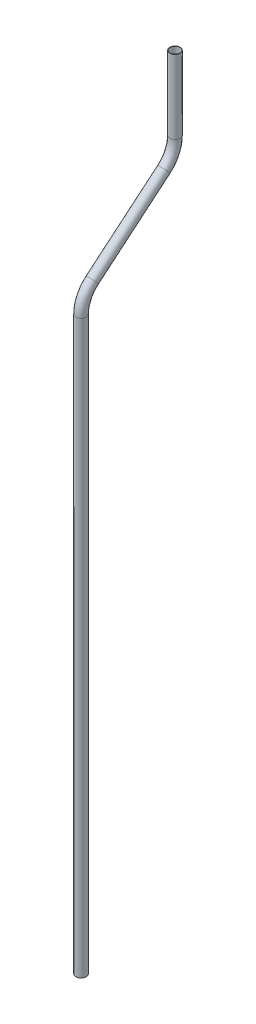
SolidWorks part; units mm, degrees
ref_plane "Front Plane" through (0, 0, 0) normal (0, 0, 1) x (1, 0, 0)
ref_plane "Top Plane" through (0, 0, 0) normal (0, 1, 0) x (1, 0, 0)
ref_plane "Right Plane" through (0, 0, 0) normal (1, 0, 0) x (0, 0, -1)
sketch "Sketch1" plane through (0, 0, 0) normal (0, 1, 0) x (1, 0, 0)
  circle A0 centre (0, 0) radius 6.35
  circle A1 centre (0, 0) radius 5.969
  dimension "D1" = 12.7
  dimension "D2" = 11.938
sketch "Sketch2" plane through (0, 0, 0) normal (1, 0, 0) x (0, 0, -1)
  line L0 (0, 0) -> (0, 698.5)
  line L1 (13.6098, 727.6863) -> (101.1687, 801.1569)
  line L2 (114.7785, 830.3432) -> (114.7785, 920.5132)
  arc A0 (0, 698.5) -> (13.6098, 727.6863) centre (38.1, 698.5) cw
  arc A1 (101.1687, 801.1569) -> (114.7785, 830.3432) centre (76.6785, 830.3432) ccw
  dimension "D3" = 38.1
  dimension "D5" = 38.1
  dimension "D1" = 698.5
  dimension "D2" = 130
  dimension "D4" = 130
  dimension "D6" = 90.17
  dimension "D7" = 114.3
sweep "Sweep2" add profiles "Sketch1" path "Sketch2"
